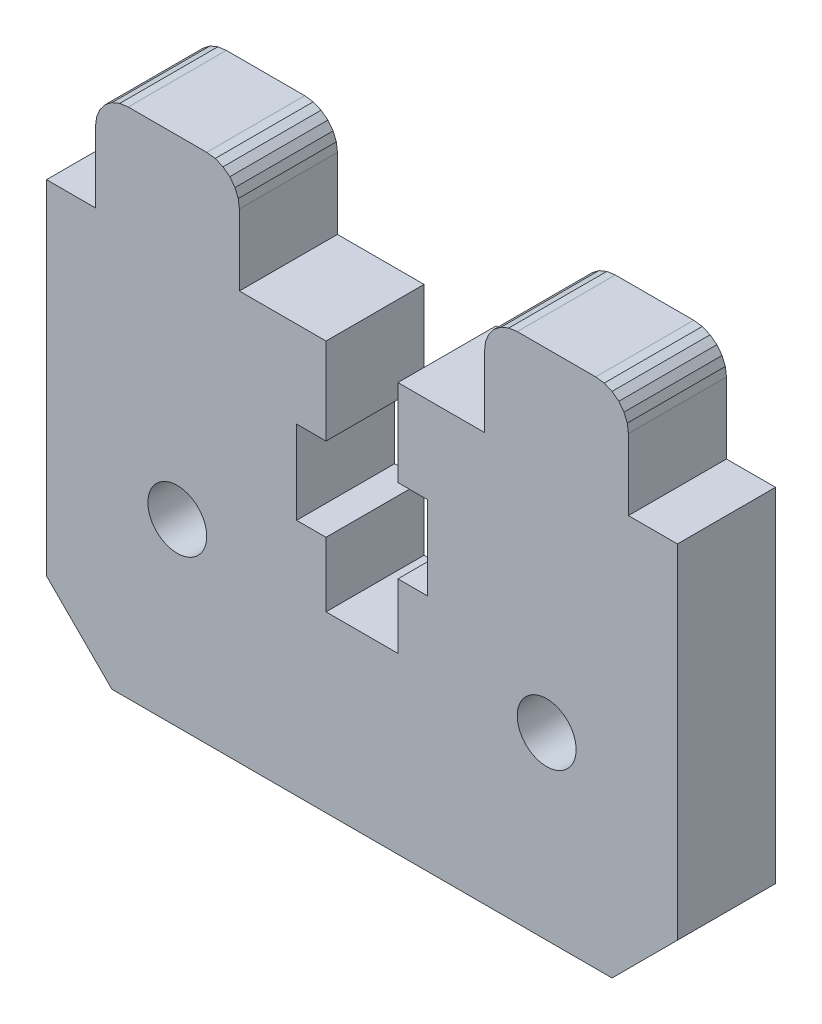
SolidWorks part; units mm, degrees
ref_plane "Plano frontal" through (0, 0, 0) normal (0, 0, 1) x (1, 0, 0)
ref_plane "Plano superior" through (0, 0, 0) normal (0, 1, 0) x (1, 0, 0)
ref_plane "Plano direito" through (0, 0, 0) normal (1, 0, 0) x (0, 0, -1)
sketch "Model" plane through (0, 0, 0) normal (0, 0, 1) x (1, 0, 0)
  line L0 (53.0414, 36.8841) -> (53.4556, 37.202)
  line L1 (59.7733, 37.4018) -> (59.2556, 37.4699)
  line L2 (28.7238, 35.9876) -> (28.9236, 36.4699)
  line L3 (37.4556, 35.4699) -> (37.3875, 35.9876)
  line L4 (36.8698, 36.8841) -> (36.4556, 37.202)
  line L5 (29.6556, 6.1199) -> (60.2556, 6.1199)
  line L6 (60.2556, 6.1199) -> (64.2556, 10.1199)
  line L7 (64.2556, 31.1199) -> (64.2556, 10.1199)
  line L8 (61.2556, 31.1199) -> (64.2556, 31.1199)
  line L9 (61.2556, 35.4699) -> (61.2556, 31.1199)
  line L10 (61.2556, 35.4699) -> (61.1875, 35.9876)
  line L11 (61.1875, 35.9876) -> (60.9877, 36.4699)
  line L12 (60.9877, 36.4699) -> (60.6698, 36.8841)
  line L13 (60.6698, 36.8841) -> (60.2556, 37.202)
  line L14 (60.2556, 37.202) -> (59.7733, 37.4018)
  line L15 (54.4556, 37.4699) -> (59.2556, 37.4699)
  line L16 (53.938, 37.4018) -> (54.4556, 37.4699)
  line L17 (53.4556, 37.202) -> (53.938, 37.4018)
  line L18 (52.7236, 36.4699) -> (53.0414, 36.8841)
  line L19 (52.5238, 35.9876) -> (52.7236, 36.4699)
  line L20 (52.4556, 35.4699) -> (52.5238, 35.9876)
  line L21 (52.4556, 31.1199) -> (52.4556, 35.4699)
  line L22 (47.1556, 31.1199) -> (52.4556, 31.1199)
  line L23 (47.1556, 25.8199) -> (47.1556, 31.1199)
  line L24 (48.9556, 25.8199) -> (47.1556, 25.8199)
  line L25 (48.9556, 20.7199) -> (48.9556, 25.8199)
  line L26 (47.1556, 20.7199) -> (48.9556, 20.7199)
  line L27 (47.1556, 16.7699) -> (47.1556, 20.7199)
  line L28 (42.7556, 16.7699) -> (47.1556, 16.7699)
  line L29 (42.7556, 20.7199) -> (42.7556, 16.7699)
  line L30 (40.9556, 20.7199) -> (42.7556, 20.7199)
  line L31 (40.9556, 25.8199) -> (40.9556, 20.7199)
  line L32 (42.7556, 25.8199) -> (40.9556, 25.8199)
  line L33 (42.7556, 31.1199) -> (42.7556, 25.8199)
  line L34 (37.4556, 31.1199) -> (42.7556, 31.1199)
  line L35 (37.4556, 35.4699) -> (37.4556, 31.1199)
  line L36 (37.3875, 35.9876) -> (37.1877, 36.4699)
  line L37 (37.1877, 36.4699) -> (36.8698, 36.8841)
  line L38 (36.4556, 37.202) -> (35.9733, 37.4018)
  line L39 (35.9733, 37.4018) -> (35.4556, 37.4699)
  line L40 (30.6556, 37.4699) -> (35.4556, 37.4699)
  line L41 (30.138, 37.4018) -> (30.6556, 37.4699)
  line L42 (29.6556, 37.202) -> (30.138, 37.4018)
  line L43 (29.2414, 36.8841) -> (29.6556, 37.202)
  line L44 (28.9236, 36.4699) -> (29.2414, 36.8841)
  line L45 (28.6556, 35.4699) -> (28.7238, 35.9876)
  line L46 (28.6556, 31.1199) -> (28.6556, 35.4699)
  line L47 (28.6556, 31.1199) -> (25.6556, 31.1199)
  line L48 (25.6556, 31.1199) -> (25.6556, 10.1199)
  line L49 (29.6556, 6.1199) -> (25.6556, 10.1199)
  circle A0 centre (56.2556, 17.1199) radius 1.8
  circle A1 centre (33.6556, 17.1199) radius 1.8
extrude "Ressalto-extrusão1" add sketch "Model" along normal blind 6
